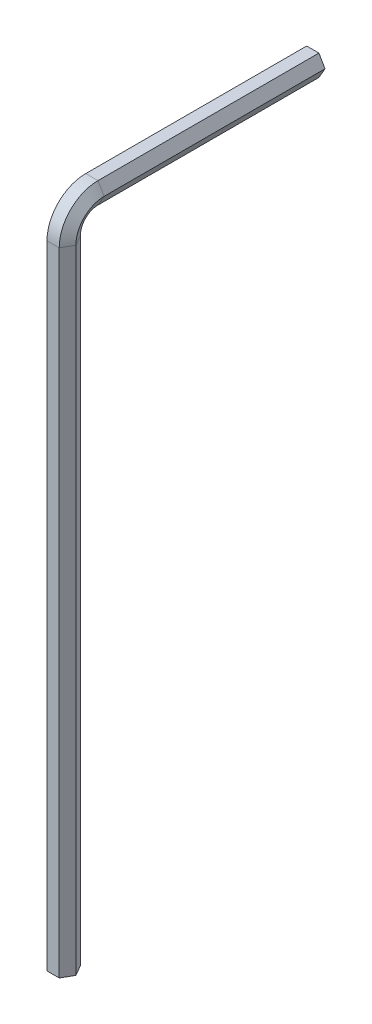
SolidWorks part; units mm, degrees
ref_plane "Front Plane" through (0, 0, 0) normal (0, 0, 1) x (1, 0, 0)
ref_plane "Top Plane" through (0, 0, 0) normal (0, 1, 0) x (1, 0, 0)
ref_plane "Right Plane" through (0, 0, 0) normal (1, 0, 0) x (0, 0, -1)
sketch "Sketch1" plane through (0, 0, 0) normal (0, 1, 0) x (1, 0, 0)
  line L1 (0.866, 0) -> (0.433, 0.75)
  line L2 (0.433, 0.75) -> (-0.433, 0.75)
  line L3 (-0.433, 0.75) -> (-0.866, 0)
  line L4 (-0.866, 0) -> (-0.433, -0.75)
  line L5 (-0.433, -0.75) -> (0.433, -0.75)
  line L6 (0.433, -0.75) -> (0.866, 0)
  circle A0 centre (0, 0) radius 0.75 construction
  dimension "D1" = 1.5
sketch "Sketch2" plane through (0, 0, 0) normal (-1, 0, 0) x (0, 0, 1)
  line L0 (0, 0) -> (0, 44.8)
  line L1 (-2, 46.8) -> (-17.65, 46.8)
  arc A0 (0, 44.8) -> (-2, 46.8) centre (-2, 44.8) ccw
  point P6 (0, 46.8)
  dimension "D3" = 2
  dimension "D1" = 46.8
  dimension "D2" = 17.65
sweep "Sweep1" add profiles "Sketch1" path "Sketch2"
sketch "Sketch3" plane through (0, 0, 0) normal (0, -1, 0) x (1, 0, 0)
  circle A0 centre (0, 0) radius 0.866 construction
sketch "Sketch4" plane through (0, 0, -17.65) normal (0, 0, -1) x (-1, 0, 0)
  circle A0 centre (0, 46.8) radius 0.866 construction
